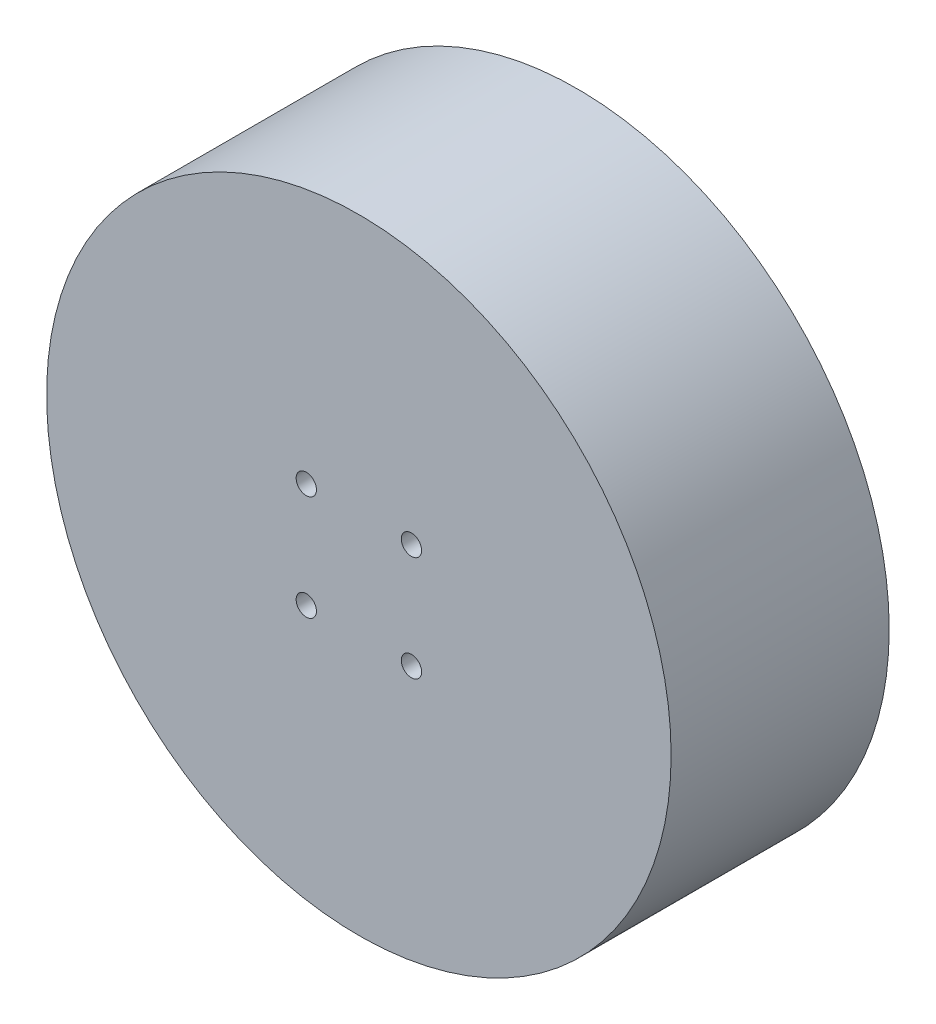
SolidWorks part; units mm, degrees
ref_plane "Front Plane" through (0, 0, 0) normal (0, 0, 1) x (1, 0, 0)
ref_plane "Top Plane" through (0, 0, 0) normal (0, 1, 0) x (1, 0, 0)
ref_plane "Right Plane" through (0, 0, 0) normal (1, 0, 0) x (0, 0, -1)
sketch "Sketch1" plane through (0, 0, 0) normal (0, 0, 1) x (1, 0, 0)
  circle A0 centre (0, 0) radius 31.5
extrude "Boss-Extrude1" add sketch "Sketch1" along normal blind 22
hole_wizard "Tap Drill for M2.5x0.45 Tap1" positions "Sketch3" profile "Sketch2" hole size "M2.5x0.45" standard "ANSI Metric"
sketch "Sketch3" plane through (0, 0, 22) normal (0, 0, 1) x (1, 0, 0)
  line L0 (0, 0) -> (-5.3033, 5.3033) construction
  line L2 (0, 0) -> (5.3033, -5.3033) construction
  line L4 (0, 0) -> (5.3033, 5.3033) construction
  line L6 (0, 0) -> (-5.3033, -5.3033) construction
  point P2 (-5.3033, 5.3033)
  point P8 (5.3033, -5.3033)
  point P13 (5.3033, 5.3033)
  point P18 (-5.3033, -5.3033)
  dimension "D1" = 15
  dimension "D2" = 15
  dimension "D3" = 7.5
  dimension "D4" = 7.5
  dimension "D5" = 7.5
  dimension "D6" = 7.5
sketch "Sketch2" plane through (-5.3033, 5.3033, 22) normal (1, 0, 0) x (0, -1, 0)
  line L0 (0, 0) -> (0, 6.1159)
  line L1 (0, 6.1159) -> (1.025, 5.5)
  line L2 (1.025, 5.5) -> (1.025, 0)
  line L5 (1.025, 0) -> (0, 0)
  line L10 (0, 6.1159) -> (-1.025, 5.5) construction
  line L11 (0, -6.35) -> (0, 107.95) construction
  dimension "Hole Dia." = 2.05
  dimension "Hole Depth" = 5.5
  dimension "Drill Angle" = 118
hole_wizard "Tap Drill for M3x0.5 Tap1" positions "Sketch5" profile "Sketch4" hole size "M3x0.5" standard "ANSI Metric"
sketch "Sketch5" plane through (0, 0, 0) normal (0, 0, -1) x (-1, 0, 0)
  line L0 (0, 0) -> (8.8388, 8.8388) construction
  line L2 (0, 0) -> (8.8388, -8.8388) construction
  line L4 (0, 0) -> (-8.8388, 8.8388) construction
  line L6 (0, 0) -> (-8.8388, -8.8388) construction
  point P2 (8.8388, 8.8388)
  point P8 (8.8388, -8.8388)
  point P12 (-8.8388, 8.8388)
  point P17 (-8.8388, -8.8388)
sketch "Sketch4" plane through (-8.8388, 8.8388, 0) normal (1, 0, 0) x (0, 1, 0)
  line L0 (0, 0) -> (0, 6.2511)
  line L1 (0, 6.2511) -> (1.25, 5.5)
  line L2 (1.25, 5.5) -> (1.25, 0)
  line L5 (1.25, 0) -> (0, 0)
  line L10 (0, 6.2511) -> (-1.25, 5.5) construction
  line L11 (0, -6.35) -> (0, 107.95) construction
  dimension "Hole Dia." = 2.5
  dimension "Hole Depth" = 5.5
  dimension "Drill Angle" = 118
